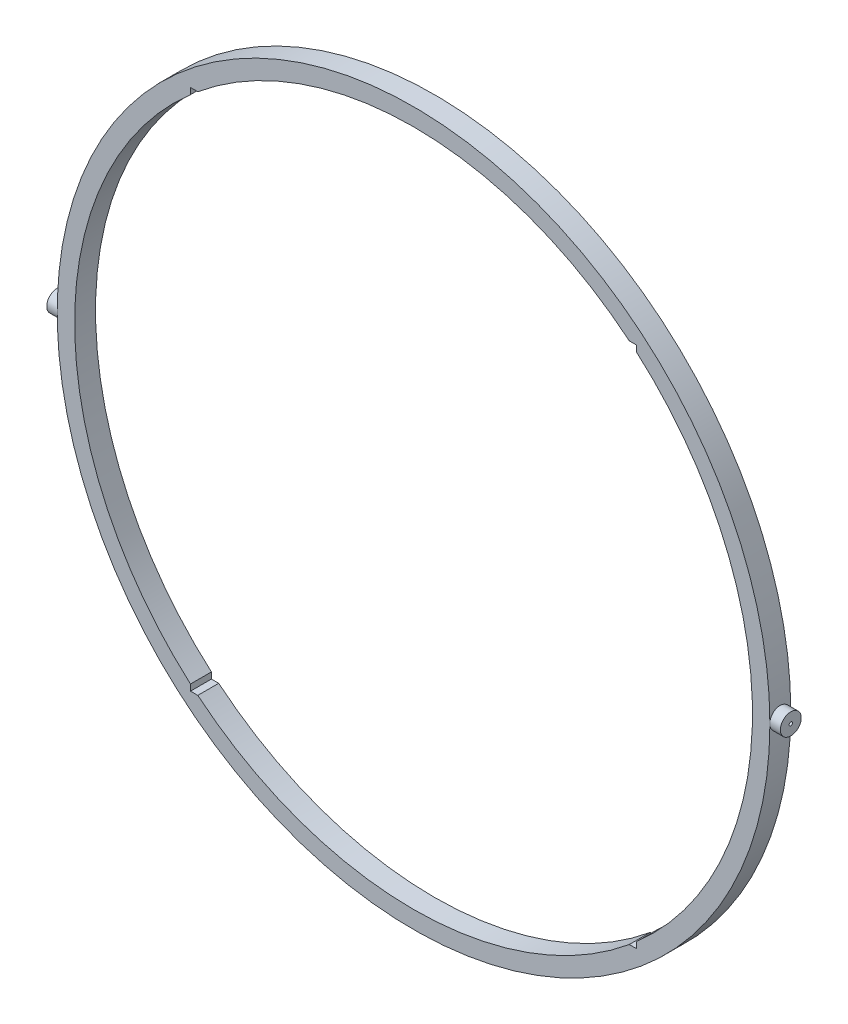
SolidWorks part; units mm, degrees
ref_plane "Front Plane" through (0, 0, 0) normal (0, 0, 1) x (1, 0, 0)
ref_plane "Top Plane" through (0, 0, 0) normal (0, 1, 0) x (1, 0, 0)
ref_plane "Right Plane" through (0, 0, 0) normal (1, 0, 0) x (0, 0, -1)
sketch "Sketch1" plane through (0, 0, 0) normal (0, 0, 1) x (1, 0, 0)
  line L0 (-64, 75) -> (-64, -75) construction
  line L1 (-64, 75) -> (64, 75) construction
  line L3 (-64, -75) -> (64, -75) construction
  line L4 (64, 75) -> (64, -75) construction
  line L5 (-64, 75) -> (64, -75) construction
  line L6 (-64, -75) -> (64, 75) construction
  circle A1 centre (0, 0) radius 97.2472
  circle A2 centre (0, 0) radius 102.2472
  point P0 (0, 0)
extrude "Boss-Extrude1" add sketch "Sketch1" along normal blind 6
ref_plane "Plane1" through (-97.2472, 0, 0) normal (1, 0, 0) x (0, 0, -1)
sketch "Sketch3" plane through (-97.2472, 0, 0) normal (1, 0, 0) x (0, 0, -1)
  line L0 (55, 0) -> (-55, 0) construction
  line L1 (0, 75) -> (0, -75) construction
  line L2 (0, -102.2472) -> (0, 102.2472) construction
  circle A2 centre (-3, 0) radius 3
  circle A3 centre (-3, 0) radius 0.5
  point P0 (3, 0)
  dimension "D2" = 3
  dimension "D1" = 3
extrude "Boss-Extrude2" add sketch "Sketch3" against normal blind 8 separate body
ref_plane "Plane4" through (97.2472, 0, 0) normal (-1, 0, 0) x (0, 0, 1)
sketch "Sketch4" plane through (97.2472, 0, 0) normal (-1, 0, 0) x (0, 0, 1)
  line L0 (0, -97.2472) -> (0, 97.2472) construction
  circle A0 centre (3, 0) radius 0.5
  circle A1 centre (3, 0) radius 3
  dimension "D1" = 3
extrude "Boss-Extrude3" add sketch "Sketch4" against normal blind 8 separate body
sketch "Sketch5" plane through (0, 0, 6) normal (0, 0, 1) x (1, 0, 0)
  line L2 (-64, 73.2189) -> (-64, 75)
  line L3 (-64, 75) -> (-61.9032, 75)
  line L5 (-64, 75) -> (64, 75) construction
  line L6 (-64, 75) -> (-64, -75) construction
  line L7 (-64, 73.2189) -> (-61.9032, 75)
  line L8 (0, 119.1146) -> (0, -121.5988) construction
  line L9 (-153.1027, 0) -> (167.3575, 0) construction
  line L10 (64, 73.2189) -> (61.9032, 75)
  line L11 (64, 73.2189) -> (64, 75)
  line L12 (64, 75) -> (61.9032, 75)
  line L13 (64, -75) -> (61.9032, -75)
  line L14 (64, -73.2189) -> (64, -75)
  line L15 (64, -73.2189) -> (61.9032, -75)
  line L16 (-64, -73.2189) -> (-61.9032, -75)
  line L17 (-64, -75) -> (-61.9032, -75)
  line L18 (-64, -73.2189) -> (-64, -75)
  circle A1 centre (0, 0) radius 97.2472 construction
extrude "Cut-Extrude3" cut sketch "Sketch5" against normal blind 10
